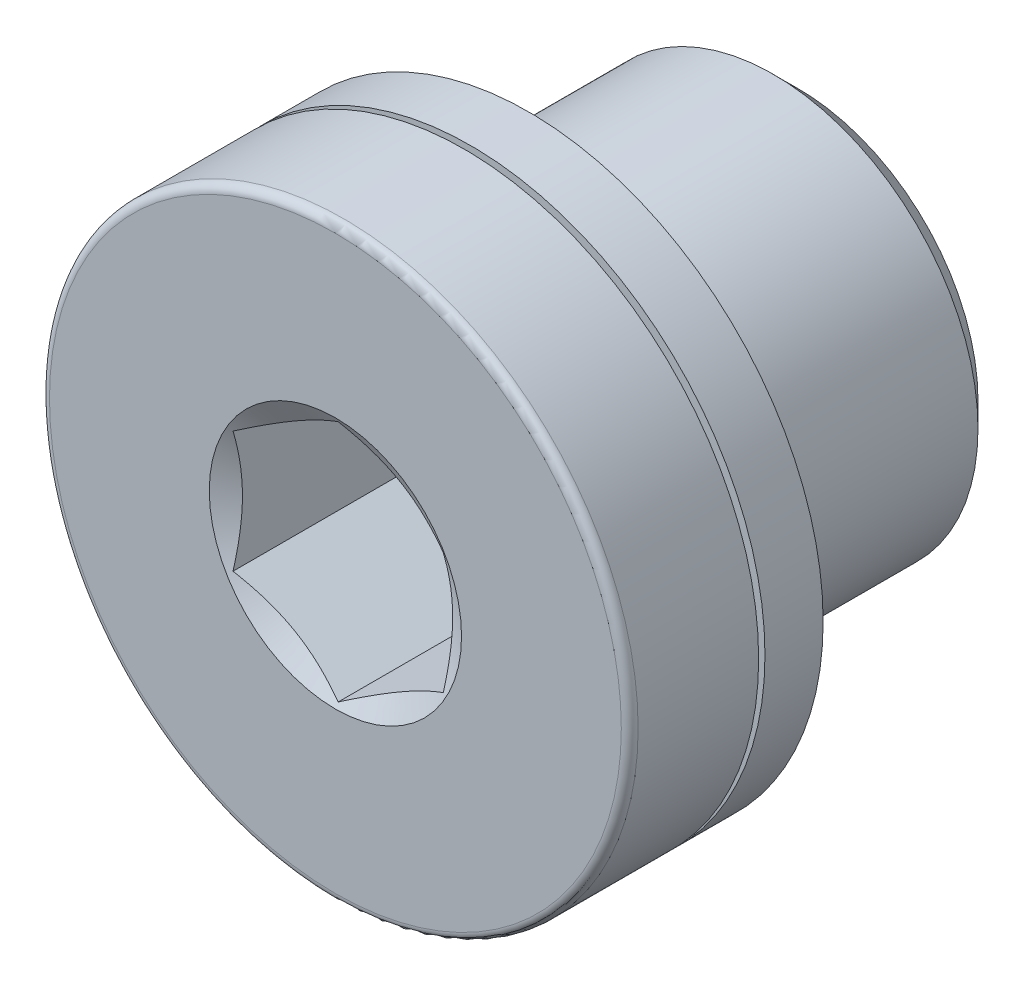
SolidWorks part; units mm, degrees
ref_plane "Front Plane" through (0, 0, 0) normal (0, 0, 1) x (1, 0, 0)
ref_plane "Top Plane" through (0, 0, 0) normal (0, 1, 0) x (1, 0, 0)
ref_plane "Right Plane" through (0, 0, 0) normal (1, 0, 0) x (0, 0, -1)
ref_plane "Plane1" through (0, 0, 0) normal (1, 0, 0) x (0, 0, -1)
sketch "Sketch1" plane through (0, 0, 0) normal (1, 0, 0) x (0, 0, -1)
  line L0 (-2.8679, 0) -> (-4.6, 3)
  line L1 (-4.6, 3) -> (-4.6, 6.8)
  line L2 (-4.4, 7) -> (-1.5333, 7)
  line L3 (-1.5333, 7) -> (-1.5333, 6.3)
  line L4 (-1.5333, 6.3) -> (-1.3833, 6.3)
  line L5 (-1.3833, 6.3) -> (-1.3833, 7)
  line L6 (-1.3833, 7) -> (0, 7)
  line L7 (0, 7) -> (0, 4.283)
  line L8 (0, 4.283) -> (0.581, 4.864)
  line L9 (0.581, 4.864) -> (5.819, 4.864)
  line L10 (5.819, 4.864) -> (6.4, 4.283)
  line L11 (6.4, 4.283) -> (6.4, 0)
  line L12 (6.4, 0) -> (-2.8679, 0)
  line L13 (6.4, 0) -> (-2.8679, 0) construction
  arc A0 (-4.6, 6.8) -> (-4.4, 7) centre (-4.4, 6.8) cw
revolve "Revolve1" add sketch "Sketch1" angle 360 about L13
cosmetic thread "Cosmetic Thread1" parameters "D1"=6.4, "D2"=8.566
ref_plane "Plane2" through (0, 0, 4.6) normal (0, 0, 1) x (1, 0, 0)
sketch "Sketch2" plane through (0, 0, 4.6) normal (0, 0, 1) x (1, 0, 0)
  line L0 (-2.5, -1.4434) -> (0, -2.8868)
  line L1 (0, -2.8868) -> (2.5, -1.4434)
  line L2 (2.5, -1.4434) -> (2.5, 1.4434)
  line L3 (2.5, 1.4434) -> (0, 2.8868)
  line L4 (0, 2.8868) -> (-2.5, 1.4434)
  line L5 (-2.5, 1.4434) -> (-2.5, -1.4434)
extrude "Cut-Extrude1" cut sketch "Sketch2" against normal blind 4.6
